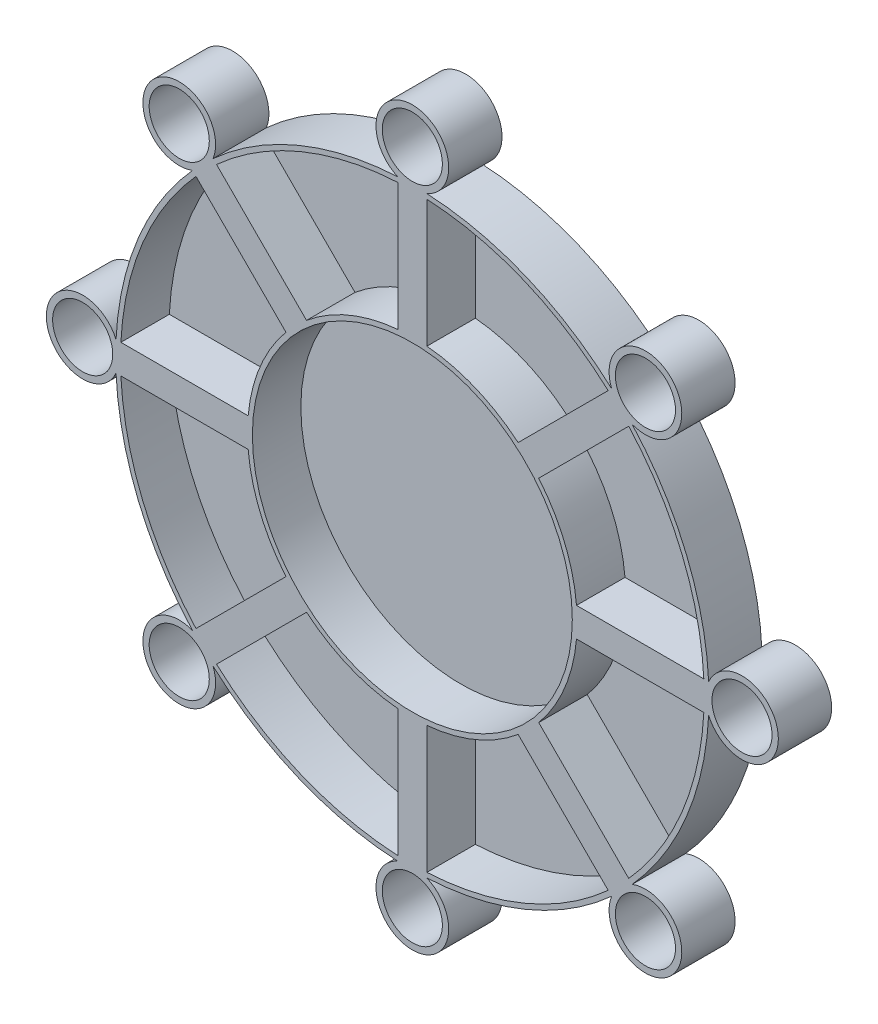
SolidWorks part; units mm, degrees
ref_plane "Alzado" through (0, 0, 0) normal (0, 0, 1) x (1, 0, 0)
ref_plane "Planta" through (0, 0, 0) normal (0, 1, 0) x (1, 0, 0)
ref_plane "Vista lateral" through (0, 0, 0) normal (1, 0, 0) x (0, 0, -1)
sketch "Croquis1" plane through (0, 0, 0) normal (0, 0, 1) x (1, 0, 0)
  line L0 (-39.7055, 55.5136) -> (-58.9803, 36.2387)
  line L1 (-35.4628, 51.271) -> (-54.7377, 31.9961)
  line L2 (-19.6807, 13.1696) -> (-46.9395, 13.1696)
  line L3 (-19.6807, 7.1696) -> (-46.9395, 7.1696)
  line L4 (-83.8069, 71.2957) -> (-83.8069, 44.037)
  line L5 (-35.4628, -30.9318) -> (-54.7377, -11.657)
  line L6 (-77.8069, 71.2957) -> (-77.8069, 44.037)
  line L7 (-39.7055, -35.1745) -> (-58.9803, -15.8996)
  line L8 (-77.8069, -50.9566) -> (-77.8069, -23.6978)
  line L9 (-83.8069, -50.9566) -> (-83.8069, -23.6978)
  line L10 (-121.9083, -35.1745) -> (-102.6334, -15.8996)
  line L11 (-126.1509, -30.9318) -> (-106.876, -11.657)
  line L12 (-141.933, 7.1696) -> (-114.6743, 7.1696)
  line L13 (-141.933, 13.1696) -> (-114.6743, 13.1696)
  line L14 (-126.1509, 51.271) -> (-106.876, 31.9961)
  line L15 (-121.9083, 55.5136) -> (-102.6334, 36.2387)
  arc A1 (-39.7055, 55.5136) -> (-35.4628, 51.271) centre (-32.7236, 58.2528) cw
  arc A2 (-83.8069, 71.2957) -> (-77.8069, 71.2957) centre (-80.8069, 78.1696) cw
  arc A3 (-19.6807, 13.1696) -> (-19.6807, 7.1696) centre (-12.8069, 10.1696) cw
  arc A4 (-35.4628, -30.9318) -> (-39.7055, -35.1745) centre (-32.7236, -37.9137) cw
  arc A5 (-77.8069, -50.9566) -> (-83.8069, -50.9566) centre (-80.8069, -57.8304) cw
  arc A6 (-121.9083, -35.1745) -> (-126.1509, -30.9318) centre (-128.8901, -37.9137) cw
  arc A7 (-141.933, 7.1696) -> (-141.933, 13.1696) centre (-148.8069, 10.1696) cw
  arc A8 (-126.1509, 51.271) -> (-121.9083, 55.5136) centre (-128.8901, 58.2528) cw
  arc A10 (-102.6334, 36.2387) -> (-83.8069, 44.037) centre (-80.8069, 10.1696) cw
  arc A11 (-77.8069, 44.037) -> (-58.9803, 36.2387) centre (-80.8069, 10.1696) cw
  arc A12 (-54.7377, 31.9961) -> (-46.9395, 13.1696) centre (-80.8069, 10.1696) cw
  arc A13 (-46.9395, 7.1696) -> (-54.7377, -11.657) centre (-80.8069, 10.1696) cw
  arc A14 (-58.9803, -15.8996) -> (-77.8069, -23.6978) centre (-80.8069, 10.1696) cw
  arc A15 (-83.8069, -23.6978) -> (-102.6334, -15.8996) centre (-80.8069, 10.1696) cw
  arc A16 (-106.876, -11.657) -> (-114.6743, 7.1696) centre (-80.8069, 10.1696) cw
  arc A17 (-114.6743, 13.1696) -> (-106.876, 31.9961) centre (-80.8069, 10.1696) cw
  point P44 (-80.8069, 10.1696)
  dimension "D1" = 8
extrude "Saliente-Extruir1" add sketch "Croquis1" along normal blind 11
sketch "Croquis2" plane through (0, 0, 11) normal (0, 0, 1) x (1, 0, 0)
  circle A0 centre (-80.8069, 10.1696) radius 33
  circle A1 centre (-128.8901, 58.2528) radius 6.2
  circle A2 centre (-80.8069, 78.1696) radius 6.2
  circle A3 centre (-32.7236, 58.2528) radius 6.2
  circle A4 centre (-12.8069, 10.1696) radius 6.2
  circle A5 centre (-32.7236, -37.9137) radius 6.2
  circle A6 centre (-80.8069, -57.8304) radius 6.2
  circle A7 centre (-128.8901, -37.9137) radius 6.2
  circle A8 centre (-148.8069, 10.1696) radius 6.2
  point P22 (-80.8069, 10.1696)
  dimension "D1" = 8
extrude "Cortar-Extruir1" cut sketch "Croquis2" against normal blind 10
sketch "Croquis3" plane through (0, 0, 0) normal (0, 0, -1) x (-1, 0, 0)
  line L0 (114.6743, 7.1696) -> (141.933, 7.1696)
  line L1 (106.876, -11.657) -> (126.1509, -30.9318)
  line L2 (102.6334, -15.8996) -> (121.9083, -35.1745)
  line L3 (83.8069, -23.6978) -> (83.8069, -50.9566)
  line L4 (77.8069, -23.6978) -> (77.8069, -50.9566)
  line L5 (58.9803, -15.8996) -> (39.7055, -35.1745)
  line L6 (54.7377, -11.657) -> (35.4628, -30.9318)
  line L7 (46.9395, 7.1696) -> (19.6807, 7.1696)
  line L8 (46.9395, 13.1696) -> (19.6807, 13.1696)
  line L9 (54.7377, 31.9961) -> (35.4628, 51.271)
  line L10 (58.9803, 36.2387) -> (39.7055, 55.5136)
  line L11 (77.8069, 44.037) -> (77.8069, 71.2957)
  line L12 (83.8069, 44.037) -> (83.8069, 71.2957)
  line L13 (102.6334, 36.2387) -> (121.9083, 55.5136)
  line L14 (106.876, 31.9961) -> (126.1509, 51.271)
  line L15 (114.6743, 13.1696) -> (141.933, 13.1696)
  arc A0 (114.6743, 7.1696) -> (106.876, -11.657) centre (80.8069, 10.1696) cw
  arc A1 (102.6334, -15.8996) -> (83.8069, -23.6978) centre (80.8069, 10.1696) cw
  arc A2 (141.933, 7.1696) -> (126.1509, -30.9318) centre (80.8069, 10.1696) cw
  arc A3 (121.9083, -35.1745) -> (83.8069, -50.9566) centre (80.8069, 10.1696) cw
  arc A4 (77.8069, -23.6978) -> (58.9803, -15.8996) centre (80.8069, 10.1696) cw
  arc A5 (77.8069, -50.9566) -> (39.7055, -35.1745) centre (80.8069, 10.1696) cw
  arc A6 (54.7377, -11.657) -> (46.9395, 7.1696) centre (80.8069, 10.1696) cw
  arc A7 (35.4628, -30.9318) -> (19.6807, 7.1696) centre (80.8069, 10.1696) cw
  arc A8 (46.9395, 13.1696) -> (54.7377, 31.9961) centre (80.8069, 10.1696) cw
  arc A9 (19.6807, 13.1696) -> (35.4628, 51.271) centre (80.8069, 10.1696) cw
  arc A10 (58.9803, 36.2387) -> (77.8069, 44.037) centre (80.8069, 10.1696) cw
  arc A11 (39.7055, 55.5136) -> (77.8069, 71.2957) centre (80.8069, 10.1696) cw
  arc A12 (83.8069, 44.037) -> (102.6334, 36.2387) centre (80.8069, 10.1696) cw
  arc A13 (83.8069, 71.2957) -> (121.9083, 55.5136) centre (80.8069, 10.1696) cw
  arc A14 (106.876, 31.9961) -> (114.6743, 13.1696) centre (80.8069, 10.1696) cw
  arc A15 (126.1509, 51.271) -> (141.933, 13.1696) centre (80.8069, 10.1696) cw
  point P40 (80.8069, 10.1696)
  dimension "D1" = 8
extrude "Saliente-Extruir2" add sketch "Croquis3" against normal blind 1
sketch "Croquis4" plane through (0, 0, 1) normal (0, 0, 1) x (1, 0, 0)
  line L0 (-126.1509, -30.9318) -> (-125.4438, -30.2247)
  line L2 (-106.876, -11.657) -> (-126.1509, -30.9318) construction
  line L3 (-141.933, 7.1696) -> (-140.933, 7.1696)
  line L4 (-141.933, 7.1696) -> (-114.6743, 7.1696) construction
  line L5 (-141.933, 13.1696) -> (-140.933, 13.1696)
  line L6 (-126.1509, 51.271) -> (-125.4438, 50.5638)
  line L7 (-121.9083, 55.5136) -> (-121.2011, 54.8065)
  line L8 (-83.8069, 71.2957) -> (-83.8069, 70.2957)
  line L9 (-77.8069, 71.2957) -> (-77.8069, 70.2957)
  line L10 (-39.7055, 55.5136) -> (-40.4126, 54.8065)
  line L11 (-35.4628, 51.271) -> (-36.1699, 50.5638)
  line L12 (-19.6807, 13.1696) -> (-20.6807, 13.1696)
  line L13 (-19.6807, 7.1696) -> (-20.6807, 7.1696)
  line L14 (-35.4628, -30.9318) -> (-36.1699, -30.2247)
  line L15 (-39.7055, -35.1745) -> (-40.4126, -34.4674)
  line L16 (-77.8069, -50.9566) -> (-77.8069, -49.9566)
  line L17 (-83.8069, -50.9566) -> (-83.8069, -49.9566)
  line L18 (-121.9083, -35.1745) -> (-121.2011, -34.4674)
  arc A0 (-126.1509, -30.9318) -> (-141.933, 7.1696) centre (-80.8069, 10.1696) cw
  arc A1 (-141.933, 13.1696) -> (-126.1509, 51.271) centre (-80.8069, 10.1696) cw
  arc A2 (-125.4438, -30.2247) -> (-140.933, 7.1696) centre (-80.8069, 10.1696) cw
  arc A3 (-140.933, 13.1696) -> (-125.4438, 50.5638) centre (-80.8069, 10.1696) cw
  arc A4 (-121.9083, 55.5136) -> (-83.8069, 71.2957) centre (-80.8069, 10.1696) cw
  arc A5 (-121.2011, 54.8065) -> (-83.8069, 70.2957) centre (-80.8069, 10.1696) cw
  arc A6 (-77.8069, 71.2957) -> (-39.7055, 55.5136) centre (-80.8069, 10.1696) cw
  arc A7 (-77.8069, 70.2957) -> (-40.4126, 54.8065) centre (-80.8069, 10.1696) cw
  arc A8 (-35.4628, 51.271) -> (-19.6807, 13.1696) centre (-80.8069, 10.1696) cw
  arc A9 (-36.1699, 50.5638) -> (-20.6807, 13.1696) centre (-80.8069, 10.1696) cw
  arc A10 (-19.6807, 7.1696) -> (-35.4628, -30.9318) centre (-80.8069, 10.1696) cw
  arc A11 (-20.6807, 7.1696) -> (-36.1699, -30.2247) centre (-80.8069, 10.1696) cw
  arc A12 (-39.7055, -35.1745) -> (-77.8069, -50.9566) centre (-80.8069, 10.1696) cw
  arc A13 (-40.4126, -34.4674) -> (-77.8069, -49.9566) centre (-80.8069, 10.1696) cw
  arc A14 (-83.8069, -50.9566) -> (-121.9083, -35.1745) centre (-80.8069, 10.1696) cw
  arc A15 (-83.8069, -49.9566) -> (-121.2011, -34.4674) centre (-80.8069, 10.1696) cw
  point P42 (-80.8069, 10.1696)
  dimension "D1" = 8
extrude "Saliente-Extruir3" add sketch "Croquis4" along normal blind 10
